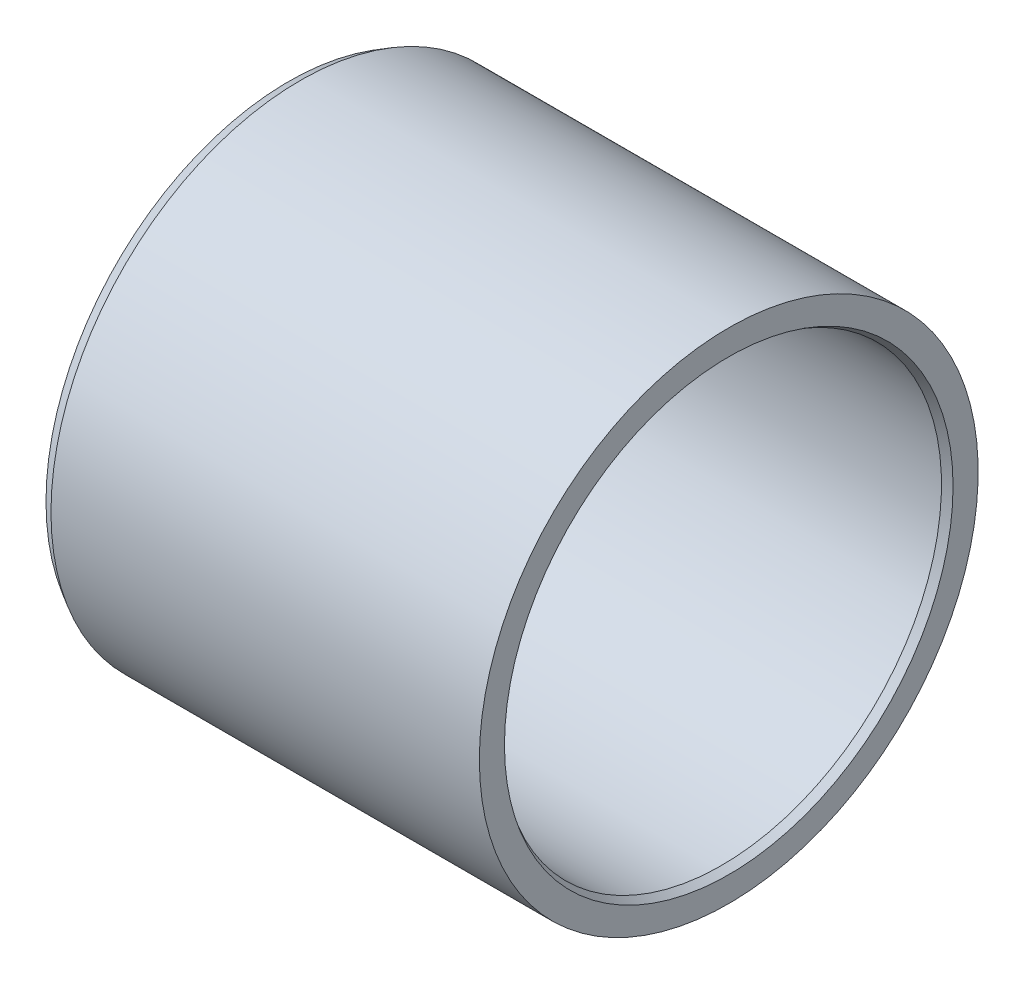
SolidWorks part; units mm, degrees
ref_plane "Vorne" through (0, 0, 0) normal (0, 0, 1) x (1, 0, 0)
ref_plane "Oben" through (0, 0, 0) normal (0, 1, 0) x (1, 0, 0)
ref_plane "Rechts" through (0, 0, 0) normal (1, 0, 0) x (0, 0, -1)
sketch "Skizze1" plane through (0, 0, 0) normal (0, 1, 0) x (1, 0, 0)
  line L0 (-14.2, 17) -> (15, 17)
  line L1 (15, 17) -> (15, 15.2887)
  line L2 (15, 15.2887) -> (14.5, 15)
  line L3 (14.5, 15) -> (-15, 15)
  line L4 (-15, 15) -> (-15, 16.5381)
  line L5 (-15, 16.5381) -> (-14.2, 17)
  line L6 (-15, 0) -> (15, 0) construction
  dimension "D1" = 0.8
  dimension "D2" = 30
  dimension "D3" = 30
  dimension "D4" = 0.5
  dimension "D5" = 30
  dimension "D6" = 15
  dimension "D7" = 17
  dimension "D8" = 15
revolve "Rotation1" add sketch "Skizze1" angle 360 about L6
equation "\"D8@Skizze1\"=\"D5@Skizze1\"/2"
